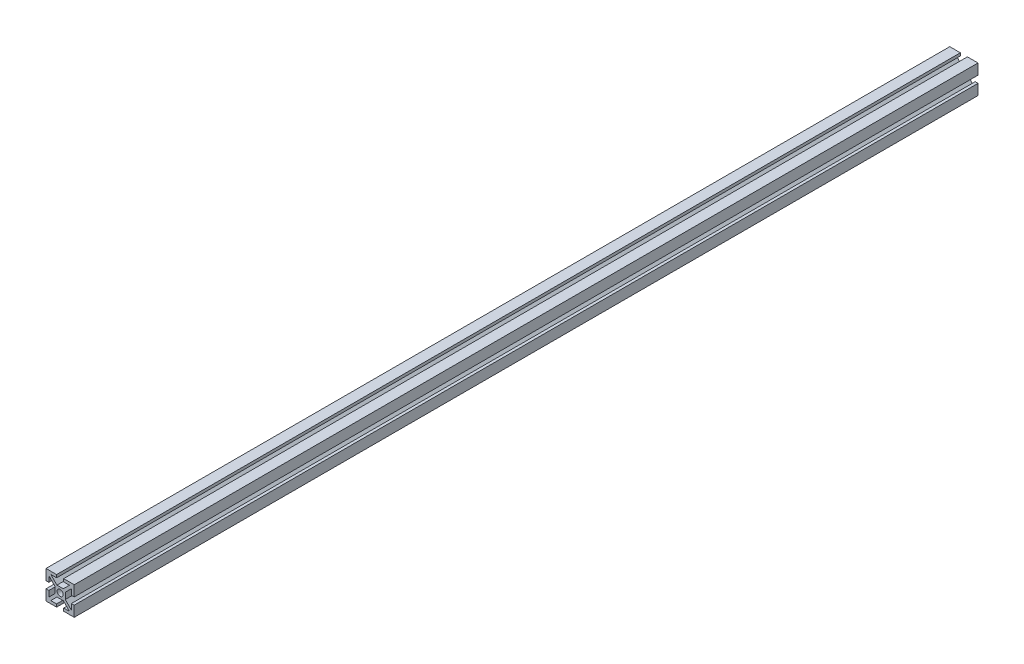
SolidWorks part; units mm, degrees
material "6061-T6 (SS)"
ref_plane "Plan de face" through (0, 0, 0) normal (0, 0, 1) x (1, 0, 0)
ref_plane "Plan de dessus" through (0, 0, 0) normal (0, 1, 0) x (1, 0, 0)
ref_plane "Plan de droite" through (0, 0, 0) normal (1, 0, 0) x (0, 0, -1)
sketch "Esquisse1" plane through (0, 0, 0) normal (0, 0, 1) x (1, 0, 0)
  line L0 (0, 0) -> (0, 68.6636) construction
  line L1 (-10, 10) -> (10, 10)
  line L2 (-10, 10) -> (-10, -10)
  line L3 (-10, -10) -> (10, -10)
  line L4 (10, 10) -> (10, -10)
  line L5 (-3.65, 3.65) -> (3.65, 3.65)
  line L6 (-3.65, 3.65) -> (-3.65, -3.65)
  line L7 (-3.65, -3.65) -> (3.65, -3.65)
  line L8 (3.65, 3.65) -> (3.65, -3.65)
  line L9 (0, 68.6636) -> (0, 0) construction
  line L10 (0, 0) -> (78.2836, 0) construction
  line L11 (-10, 10) -> (10, -10) construction
  line L12 (-2.5, 10) -> (2.5, 10)
  line L13 (-2.5, 10) -> (-2.5, 8)
  line L14 (-2.5, 8) -> (2.5, 8)
  line L15 (2.5, 10) -> (2.5, 8)
  line L16 (10, 2.5) -> (8, 2.5)
  line L17 (10, 2.5) -> (10, -2.5)
  line L18 (10, -2.5) -> (8, -2.5)
  line L19 (8, 2.5) -> (8, -2.5)
  line L20 (2.5, -10) -> (-2.5, -10)
  line L21 (2.5, -10) -> (2.5, -8)
  line L22 (2.5, -8) -> (-2.5, -8)
  line L23 (-2.5, -10) -> (-2.5, -8)
  line L24 (-10, -2.5) -> (-8, -2.5)
  line L25 (-10, -2.5) -> (-10, 2.5)
  line L26 (-10, 2.5) -> (-8, 2.5)
  line L27 (-8, -2.5) -> (-8, 2.5)
  line L28 (10, 10) -> (-10, -10) construction
  line L29 (-8, 2.5) -> (-8, 6.5858)
  line L30 (-8, 6.5858) -> (-3.65, 2.2358)
  line L31 (-3.65, 2.2358) -> (-3.65, -2.2358)
  line L32 (-3.65, -2.2358) -> (-8, -6.5858)
  line L33 (-8, -6.5858) -> (-8, -2.5)
  line L34 (-2.5, -8) -> (-6.5858, -8)
  line L35 (-6.5858, -8) -> (-2.2358, -3.65)
  line L36 (-2.2358, -3.65) -> (2.2358, -3.65)
  line L37 (2.2358, -3.65) -> (6.5858, -8)
  line L38 (6.5858, -8) -> (2.5, -8)
  line L39 (8, -6.5858) -> (3.65, -2.2358)
  line L40 (3.65, -2.2358) -> (3.65, 2.2358)
  line L41 (3.65, 2.2358) -> (8, 6.5858)
  line L42 (8, 6.5858) -> (8, 2.5)
  line L43 (8, 2.5) -> (8.0085, 2.747)
  line L44 (8, -2.5) -> (8, -6.5858)
  line L45 (2.5, 8) -> (6.5858, 8)
  line L46 (6.5858, 8) -> (2.2358, 3.65)
  line L47 (2.2358, 3.65) -> (-2.2358, 3.65)
  line L48 (-2.2358, 3.65) -> (-6.5858, 8)
  line L49 (-6.5858, 8) -> (-2.5, 8)
  circle A0 centre (0, 0) radius 2.15
  dimension "D1" = 4.3
  dimension "D2" = 6.35
  dimension "D3" = 6.35
  dimension "D4" = 6.35
  dimension "D5" = 6.35
  dimension "D6" = 20
  dimension "D7" = 20
  dimension "D8" = 5
  dimension "D9" = 5
  dimension "D10" = 5
  dimension "D11" = 5
  dimension "D12" = 2
  dimension "D13" = 2
  dimension "D14" = 2
  dimension "D15" = 2
  dimension "D16" = 2
  dimension "D17" = 2
  dimension "D18" = 2
  dimension "D19" = 2
extrude "Boss.-Extru.1" add sketch "Esquisse1" along normal blind 640
